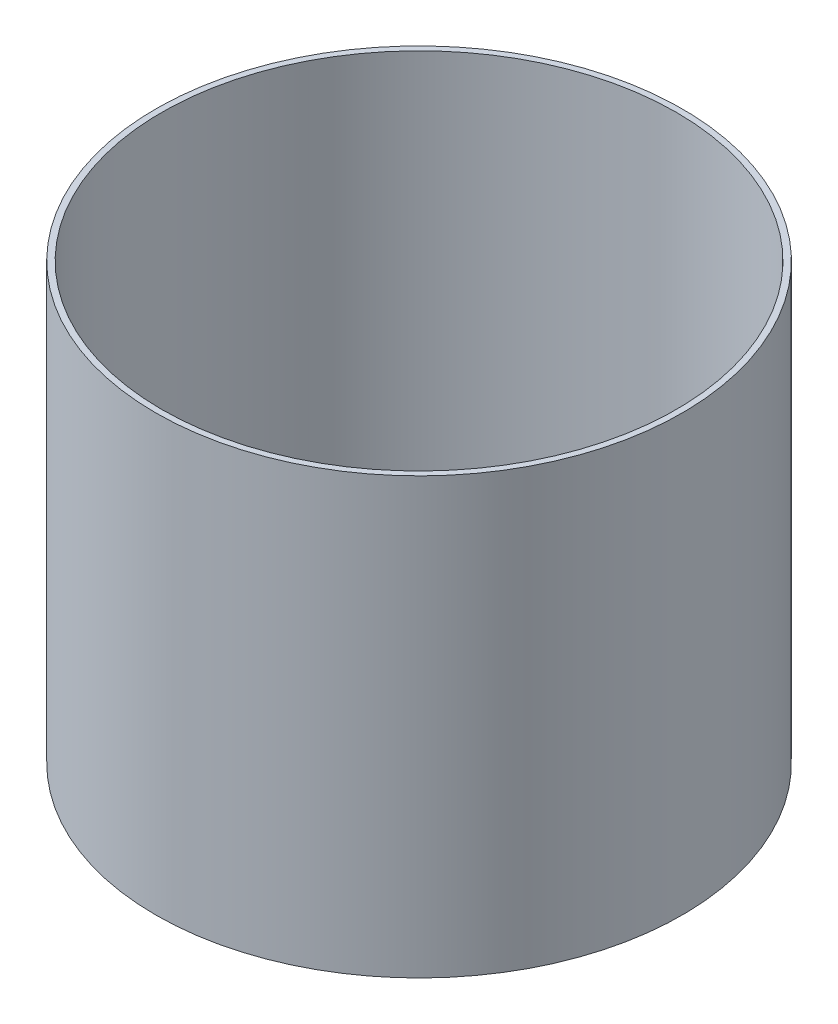
SolidWorks part; units mm, degrees
ref_plane "前视基准面" through (0, 0, 0) normal (0, 0, 1) x (1, 0, 0)
ref_plane "上视基准面" through (0, 0, 0) normal (0, 1, 0) x (1, 0, 0)
ref_plane "右视基准面" through (0, 0, 0) normal (1, 0, 0) x (0, 0, -1)
other "Configuration Table"
sketch "草图1" plane through (0, 0, 0) normal (0, 1, 0) x (1, 0, 0)
  circle A1 centre (0, 0) radius 22.1
  circle A2 centre (0, 0) radius 21.6
  dimension "D1" = 0.5
  dimension "D2" = 43.2
extrude "凸台-拉伸1" add sketch "草图1" along normal blind 36.5
